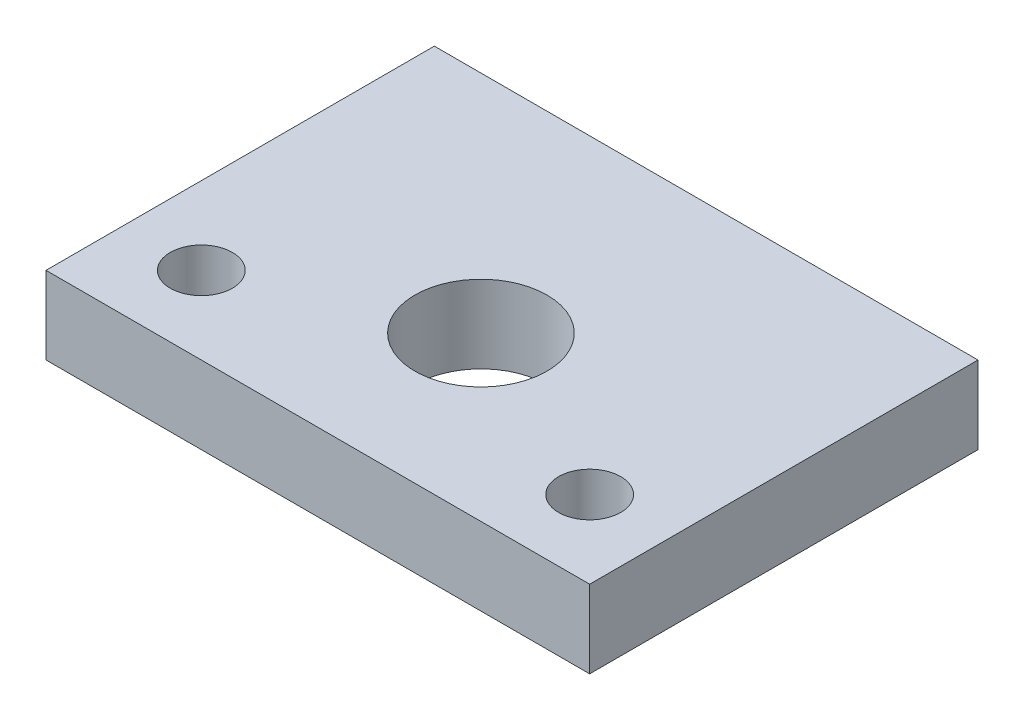
SolidWorks part; units mm, degrees
ref_plane "Front Plane" through (0, 0, 0) normal (0, 0, 1) x (1, 0, 0)
ref_plane "Top Plane" through (0, 0, 0) normal (0, 1, 0) x (1, 0, 0)
ref_plane "Right Plane" through (0, 0, 0) normal (1, 0, 0) x (0, 0, -1)
sketch "Sketch2" plane through (0, 0, 0) normal (0, 1, 0) x (1, 0, 0)
  line L1 (35, -25) -> (-35, -25)
  line L2 (35, -25) -> (35, 25)
  line L3 (35, 25) -> (-35, 25)
  line L4 (-35, -25) -> (-35, 25)
  line L5 (35, -25) -> (-35, 25) construction
  line L6 (35, 25) -> (-35, -25) construction
  point P0 (0, 0)
  dimension "D1" = 50
  dimension "D2" = 70
extrude "Boss-Extrude1" add sketch "Sketch2" along normal blind 10
sketch "Sketch3" plane through (0, 0, 0) normal (0, -1, 0) x (1, 0, 0)
  line L0 (0, 25) -> (0, -35) construction
  line L1 (-35, 25) -> (35, 25) construction
  line L2 (-35, -25) -> (-35, 25) construction
  circle A0 centre (-25, 15) radius 4
  circle A1 centre (25, 15) radius 4
  dimension "D1" = 8
  dimension "D2" = 10
  dimension "D3" = 10
  dimension "D4" = 50
extrude "Cut-Extrude1" cut sketch "Sketch3" against normal through all
sketch "Sketch4" plane through (0, 0, 25) normal (0, 0, 1) x (1, 0, 0)
  line L0 (35, 5) -> (0, 5) construction
  line L1 (35, 10) -> (35, 0) construction
  line L2 (0, 5) -> (0, 10) construction
  line L3 (-35, 10) -> (35, 10) construction
  circle A0 centre (25, 5) radius 2
  circle A1 centre (-25, 5) radius 2
  dimension "D1" = 4
  dimension "D2" = 10
extrude "Cut-Extrude2" [suppressed] cut sketch "Sketch4" against normal blind 10
sketch "Sketch5" plane through (0, 0, 0) normal (0, -1, 0) x (1, 0, 0)
  circle A0 centre (0, 4) radius 10 construction
  circle A1 centre (0, 4) radius 10
  circle A2 centre (0, 4) radius 8.5
  dimension "D1" = 17
extrude "Cut-Extrude3" cut sketch "Sketch5" against normal through all contours A2
